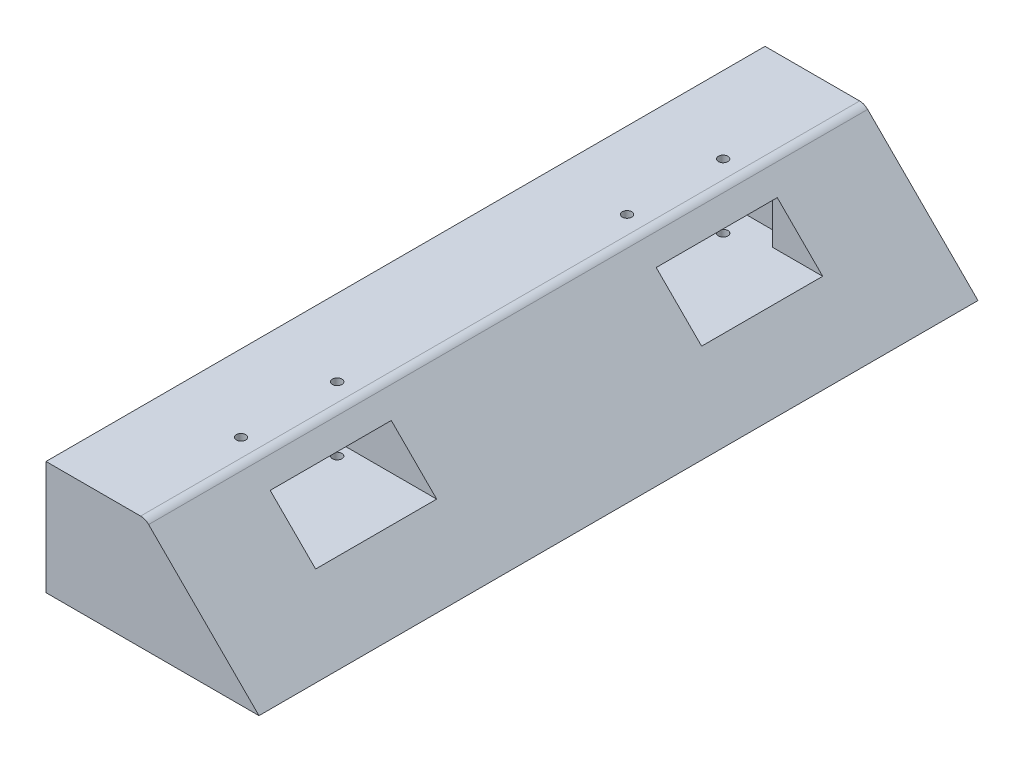
SolidWorks part; units mm, degrees
ref_plane "Alzado" through (0, 0, 0) normal (0, 0, 1) x (1, 0, 0)
ref_plane "Planta" through (0, 0, 0) normal (0, 1, 0) x (1, 0, 0)
ref_plane "Vista lateral" through (0, 0, 0) normal (1, 0, 0) x (0, 0, -1)
sketch "Croquis1" plane through (0, 0, 0) normal (0, 0, 1) x (1, 0, 0)
  line B0 (56.282, 0) -> (27.1213, 29.1606)
  line B1 (25, 30.0393) -> (0, 30.0393)
  line B2 (0, 30.0393) -> (0, 0)
  line B3 (0, 0) -> (56.282, 0)
  arc B4 (27.1213, 29.1606) -> (25, 30.0393) centre (25, 27.0393) ccw
sketch_block_instance "Bloque2-1"
sketch_block "Bloque2"
extrude "Saliente-Extruir1" add sketch "Croquis1" along normal blind 190
sketch "Croquis2" plane through (0, 0, 190) normal (0, 0, 1) x (1, 0, 0)
  line L0 (0, 30.0393) -> (0, 25.0393) construction
  line L1 (0, 30.0393) -> (0, 0) construction
  line L2 (0, 25.0393) -> (0, 13.0393) construction
  line L3 (0, 13.0393) -> (43.2426, 13.0393) construction
  line L4 (56.282, 0) -> (27.1213, 29.1606) construction
  line L5 (43.2426, 13.0393) -> (31.2426, 25.0393) construction
  line L6 (31.2426, 25.0393) -> (0, 25.0393) construction
  line L7 (31.2426, 25.0393) -> (31.2426, 0) construction
  line L8 (0, 0) -> (56.282, 0) construction
  point P13 (0, 0)
sketch "Croquis3" plane through (0, 0, 0) normal (0, -1, 0) x (1, 0, 0)
  line L0 (31.2426, 190) -> (31.2426, 0) construction
  line L1 (0, 0) -> (56.282, 0) construction
  line L2 (56.282, 95) -> (0, 95) construction
  line L3 (56.282, 162) -> (0, 162)
  line L4 (56.282, 190) -> (56.282, 0) construction
  line L5 (0, 190) -> (0, 0) construction
  line L6 (56.282, 95) -> (56.282, 60) construction
  line L7 (56.282, 60) -> (0, 60)
  line L8 (56.282, 60) -> (0, 60) construction
  line L9 (56.282, 60) -> (56.282, 28)
  line L10 (56.282, 28) -> (0, 28)
  line L11 (0, 60) -> (0, 28)
  line L12 (0, 130) -> (0, 162)
  line L13 (56.282, 130) -> (0, 130)
  line L14 (56.282, 130) -> (56.282, 162)
extrude "Cortar-Extruir1" cut sketch "Croquis3" against normal up to vertex (25.0393 mm away) up to point (31.2426, 25.0393, 190)
sketch "Croquis4" plane through (0, 0, 0) normal (0, -1, 0) x (1, 0, 0)
  line L0 (0, 95) -> (7.9289, 95) construction
  line L7 (0, 130) -> (15, 130)
  line L8 (0, 130) -> (56.282, 130) construction
  line L9 (0, 130) -> (0, 60)
  line L10 (0, 60) -> (15, 60)
  line L11 (56.282, 60) -> (0, 60) construction
  line L12 (15, 130) -> (7.9289, 122.9289)
  line L13 (15, 130) -> (15.0709, 130) construction
  line L14 (7.9289, 122.9289) -> (7.9289, 67.0711)
  line L15 (15, 60) -> (7.9289, 67.0711)
  point P0 (0, 130)
  point P2 (0, 60)
extrude "Cortar-Extruir3" cut sketch "Croquis4" against normal up to surface (25.0393 mm away) up to face at (15.6213, 25.0393, 146)
sketch "Croquis5" plane through (0, 0, 130) normal (0, 0, 1) x (1, 0, 0)
  line L0 (15, 25.0393) -> (15, 13.0393) construction
  line L1 (15, 25.0393) -> (15, 0) construction
  line L2 (56.282, 0) -> (0, 0)
  line L3 (0, 0) -> (0, 13.0393)
  line L4 (0, 13.0393) -> (43.2426, 13.0393)
  line L5 (43.2426, 13.0393) -> (56.282, 0)
extrude "Saliente-Extruir2" add sketch "Croquis5" along normal through all
sketch "Croquis6" plane through (0, 0, 130) normal (0, 0, -1) x (-1, 0, 0)
  line L0 (0, 0) -> (0, 13.0393)
  line L1 (0, 13.0393) -> (-43.2426, 13.0393)
  line L2 (-43.2426, 13.0393) -> (-56.282, 0)
  line L3 (-56.282, 0) -> (0, 0)
extrude "Saliente-Extruir3" add sketch "Croquis6" along normal through all
sketch "Croquis7" plane through (0, 0, 0) normal (-1, 0, 0) x (0, 0, 1)
  line L0 (28, 25.0393) -> (28, 13.0393) construction
  line L1 (28, 25.0393) -> (24, 25.0393)
  line L2 (28, 25.0393) -> (28, 13.0393)
  line L3 (28, 13.0393) -> (24, 13.0393)
  line L4 (24, 25.0393) -> (24, 13.0393)
  line L5 (162, 25.0393) -> (162, 13.0393) construction
  line L6 (162, 25.0393) -> (166, 25.0393)
  line L7 (162, 25.0393) -> (162, 13.0393)
  line L8 (162, 13.0393) -> (166, 13.0393)
  line L9 (166, 25.0393) -> (166, 13.0393)
  line L10 (162, 25.0393) -> (28, 25.0393) construction
extrude "Cortar-Extruir6" cut sketch "Croquis7" against normal blind 30
sketch "Croquis8" plane through (0, 13.0393, 0) normal (0, 1, 0) x (1, 0, 0)
  circle A0 centre (20.2426, -158.7) radius 1.25
  circle A1 centre (20.2426, -133.3) radius 1.25
  circle A2 centre (20.2426, -31.3) radius 1.25
  circle A3 centre (20.2426, -56.7) radius 1.25
extrude "Cortar-Extruir7" cut sketch "Croquis8" against normal through all both and the other way through all
sketch "Croquis9" plane through (0, 0, 0) normal (0, -1, 0) x (1, 0, 0)
  circle A0 centre (20.2426, 158.7) radius 3.5
  circle A1 centre (20.2426, 133.3) radius 3.5
  circle A2 centre (20.2426, 56.7) radius 3.5
  circle A3 centre (20.2426, 31.3) radius 3.5
extrude "Cortar-Extruir8" cut sketch "Croquis9" against normal blind 8
